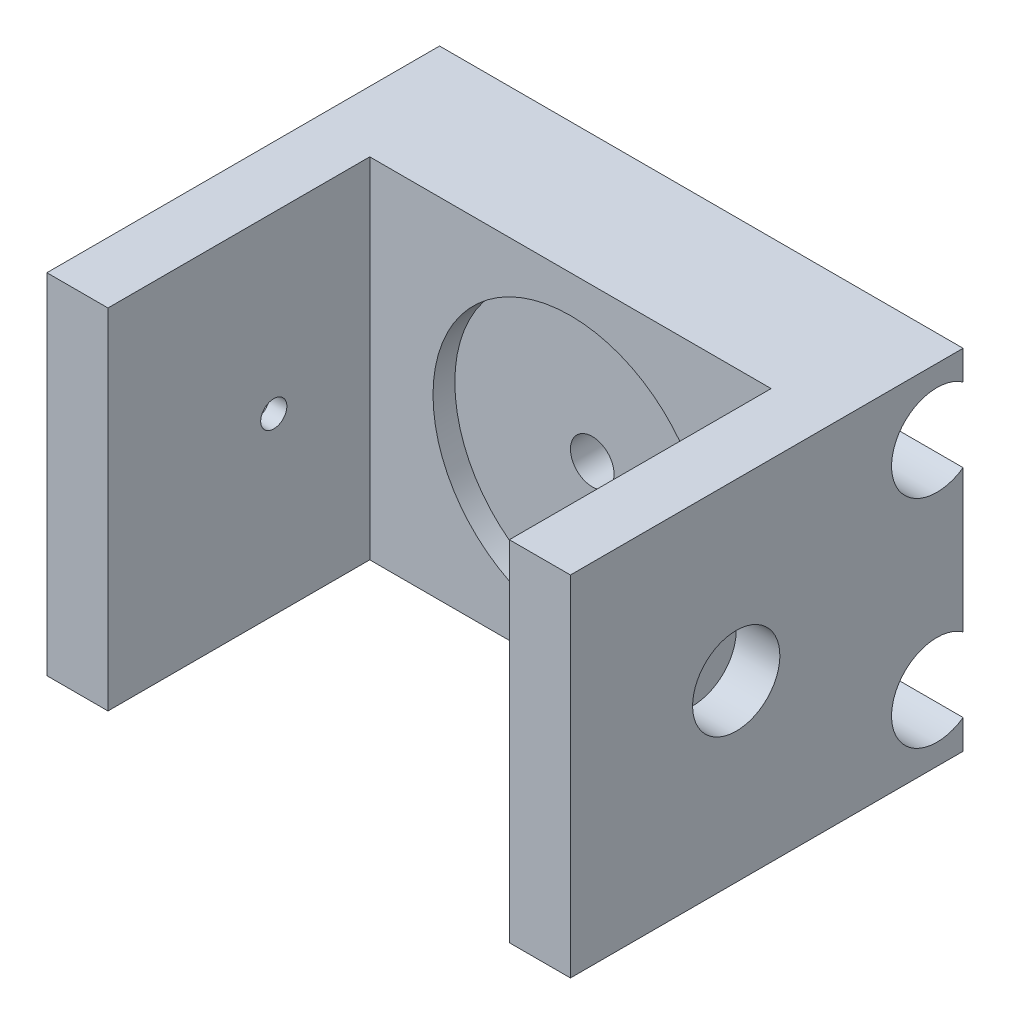
SolidWorks part; units mm, degrees
ref_plane "Front Plane" through (0, 0, 0) normal (0, 0, 1) x (1, 0, 0)
ref_plane "Top Plane" through (0, 0, 0) normal (0, 1, 0) x (1, 0, 0)
ref_plane "Right Plane" through (0, 0, 0) normal (1, 0, 0) x (0, 0, -1)
sketch "Sketch1" plane through (0, 0, 0) normal (0, 0, 1) x (1, 0, 0)
  line L1 (-17.7778, 20.915) -> (42.2222, 20.915)
  line L2 (-17.7778, 20.915) -> (-17.7778, -19.085)
  line L3 (-17.7778, -19.085) -> (42.2222, -19.085)
  line L4 (42.2222, 20.915) -> (42.2222, -19.085)
  dimension "D1" = 40
  dimension "D2" = 60
extrude "Boss-Extrude1" add sketch "Sketch1" along normal blind 15
sketch "Sketch3" plane through (42.2222, 0, 0) normal (1, 0, 0) x (0, 0, -1)
  line L0 (0, -19.085) -> (0, 20.915) construction
  line L3 (-15, 20.915) -> (0, 20.915) construction
  circle A0 centre (-3, -11.485) radius 5.2
  circle A1 centre (-3, 13.315) radius 5.2
  dimension "D1" = 3
  dimension "D2" = 3
  dimension "D3" = 24.8
  dimension "D4" = 7.6
extrude "Cut-Extrude1" cut sketch "Sketch3" against normal blind 63
sketch "Sketch4" plane through (0, 0, 15) normal (0, 0, 1) x (1, 0, 0)
  line L0 (-17.7778, -19.085) -> (42.2222, -19.085) construction
  line L6 (42.2222, 20.915) -> (35.2222, 20.915)
  line L7 (42.2222, 20.915) -> (42.2222, -19.085)
  line L8 (42.2222, -19.085) -> (35.2222, -19.085)
  line L9 (35.2222, 20.915) -> (35.2222, -19.085)
  dimension "D2" = 7
extrude "Boss-Extrude2" add sketch "Sketch4" along normal blind 30
sketch "Sketch5" plane through (42.2222, 0, 0) normal (1, 0, 0) x (0, 0, -1)
  line L0 (0, 0.915) -> (-45, 0.915) construction
  line L1 (0, -7.2376) -> (0, 9.0677) construction
  line L2 (-45, -19.085) -> (-45, 20.915) construction
  circle A0 centre (-26, 0.915) radius 5
  dimension "D1" = 19
  dimension "D2" = 10
extrude "Cut-Extrude2" cut sketch "Sketch5" against normal blind 5
ref_plane "Plane3" through (12.2222, 0, 0) normal (-1, 0, 0) x (0, 0, 1)
mirror "Mirror1" about plane through (12.2222, 0, 0) normal (-1, 0, 0) of "Cut-Extrude2", "Boss-Extrude2"
sketch "Sketch6" plane through (0, 0, 0) normal (0, 0, -1) x (-1, 0, 0)
  line L0 (-42.2222, 0.915) -> (17.7778, 0.915) construction
  line L1 (-42.2222, -7.2376) -> (-42.2222, 9.0677) construction
  line L2 (17.7778, 9.0677) -> (17.7778, -7.2376) construction
  circle A0 centre (-12.2222, 0.915) radius 5
  dimension "D1" = 10
extrude "Cut-Extrude3" cut sketch "Sketch6" against normal blind 4
sketch "Sketch7" plane through (0, 0, 4) normal (0, 0, -1) x (-1, 0, 0)
  circle A0 centre (-12.2222, 0.915) radius 2.5
  dimension "D1" = 5
extrude "Cut-Extrude4" cut sketch "Sketch7" against normal through all
sketch "Sketch8" plane through (0, 0, 15) normal (0, 0, 1) x (1, 0, 0)
  circle A0 centre (12.2222, 0.915) radius 15.75
  dimension "D1" = 31.5
extrude "Cut-Extrude5" cut sketch "Sketch8" against normal blind 2.5 contours A0
sketch "Sketch9" plane through (35.2222, 0, 0) normal (-1, 0, 0) x (0, 0, 1)
  circle A0 centre (26, 0.915) radius 1.5
  dimension "D1" = 3
extrude "Cut-Extrude6" cut sketch "Sketch9" against normal through all both and the other way through all contours A0
